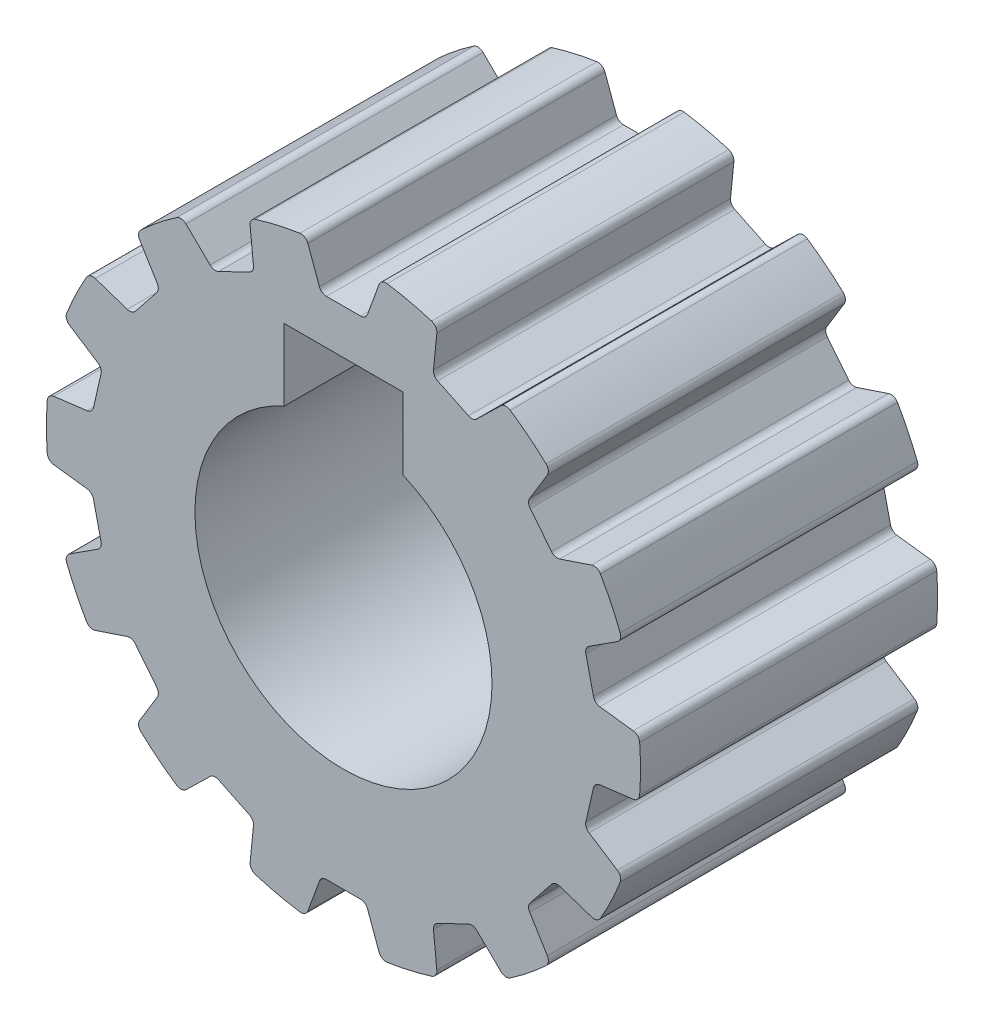
SolidWorks part; units mm, degrees
ref_plane "Front Plane" through (0, 0, 0) normal (0, 0, 1) x (1, 0, 0)
ref_plane "Top Plane" through (0, 0, 0) normal (0, 1, 0) x (1, 0, 0)
ref_plane "Right Plane" through (0, 0, 0) normal (1, 0, 0) x (0, 0, -1)
sketch "Sketch1" plane through (0, 0, 0) normal (0, 0, 1) x (1, 0, 0)
  line L0 (0, 0) -> (0, 7.8748) construction
  line L2 (-2, 7) -> (2, 7)
  line L3 (-2, 7) -> (-2, 4.5826)
  line L5 (2, 7) -> (2, 4.5826)
  circle A0 centre (0, 0) radius 10
  arc A1 (-2, 4.5826) -> (2, 4.5826) centre (0, 0) ccw
  dimension "D1" = 20
  dimension "D2" = 10
  dimension "D3" = 4
  dimension "D4" = 7
extrude "Boss-Extrude1" add sketch "Sketch1" along normal blind 10
sketch "Sketch2" plane through (0, 0, 10) normal (0, 0, 1) x (1, 0, 0)
  line L0 (0, 0) -> (0, 13.3369) construction
  line L1 (-0.75, 8.5) -> (0.75, 8.5)
  line L2 (0.75, 8.5) -> (1.2666, 9.9195)
  line L3 (-0.75, 8.5) -> (-1.2666, 9.9195)
  circle A0 centre (0, 0) radius 10 construction
  circle A1 centre (0, 0) radius 10
  point P10 (0, 0)
  circle M6 centre (0, 0) radius 10
  dimension "D1" = 1.5
  dimension "D2" = 20
  dimension "D3" = 20
  dimension "D4" = 8.5
extrude "Cut-Extrude1" cut sketch "Sketch2" against normal through all contours L1 L0 A1 L3 | L0 L1 L2 M6
pattern_circular "CirPattern1" count 14 over 360 about axis through (0, 0, 0) along (0, 0, 1) of "Cut-Extrude1"
fillet "Fillet1" radius 0.25 56 edges at (-8.5451, 5.1944, 5) (-9.3889, 3.4422, 5) (-8.12, 2.6226, 5) (-8.4538, 1.1602, 5) (-9.9526, 0.9724, 5) (-9.9526, -0.9724, 5) (-8.4538, -1.1602, 5) (-8.12, -2.6226, 5) (-9.3889, -3.4422, 5) (-8.5451, -5.1944, 5) (-7.1132, -4.7133, 5) (-6.178, -5.886, 5) (-6.9656, -7.175, 5) (-5.4451, -8.3875, 5) (-4.3637, -7.3328, 5) (-3.0123, -7.9836, 5) (-3.1627, -9.4867, 5) (-1.2666, -9.9195, 5) (-0.75, -8.5, 5) (0.75, -8.5, 5) (1.2666, -9.9195, 5) (3.1627, -9.4867, 5) (3.0123, -7.9836, 5) (4.3637, -7.3328, 5) (5.4451, -8.3875, 5) (6.9656, -7.175, 5) (6.178, -5.886, 5) (7.1132, -4.7133, 5) (8.5451, -5.1944, 5) (9.3889, -3.4422, 5) (8.12, -2.6226, 5) (8.4538, -1.1602, 5) (9.9526, -0.9724, 5) (9.9526, 0.9724, 5) (8.4538, 1.1602, 5) (8.12, 2.6226, 5) (9.3889, 3.4422, 5) (8.5451, 5.1944, 5) (7.1132, 4.7133, 5) (6.178, 5.886, 5) (5.4451, 8.3875, 5) (4.3637, 7.3328, 5) (3.0123, 7.9836, 5) (3.1627, 9.4867, 5) (1.2666, 9.9195, 5) (0.75, 8.5, 5) (-0.75, 8.5, 5) (-1.2666, 9.9195, 5) (-3.1627, 9.4867, 5) (-3.0123, 7.9836, 5) (-4.3637, 7.3328, 5) (-5.4451, 8.3875, 5) (-6.9656, 7.175, 5) (-6.178, 5.886, 5) (-7.1132, 4.7133, 5) (6.9656, 7.175, 5)
